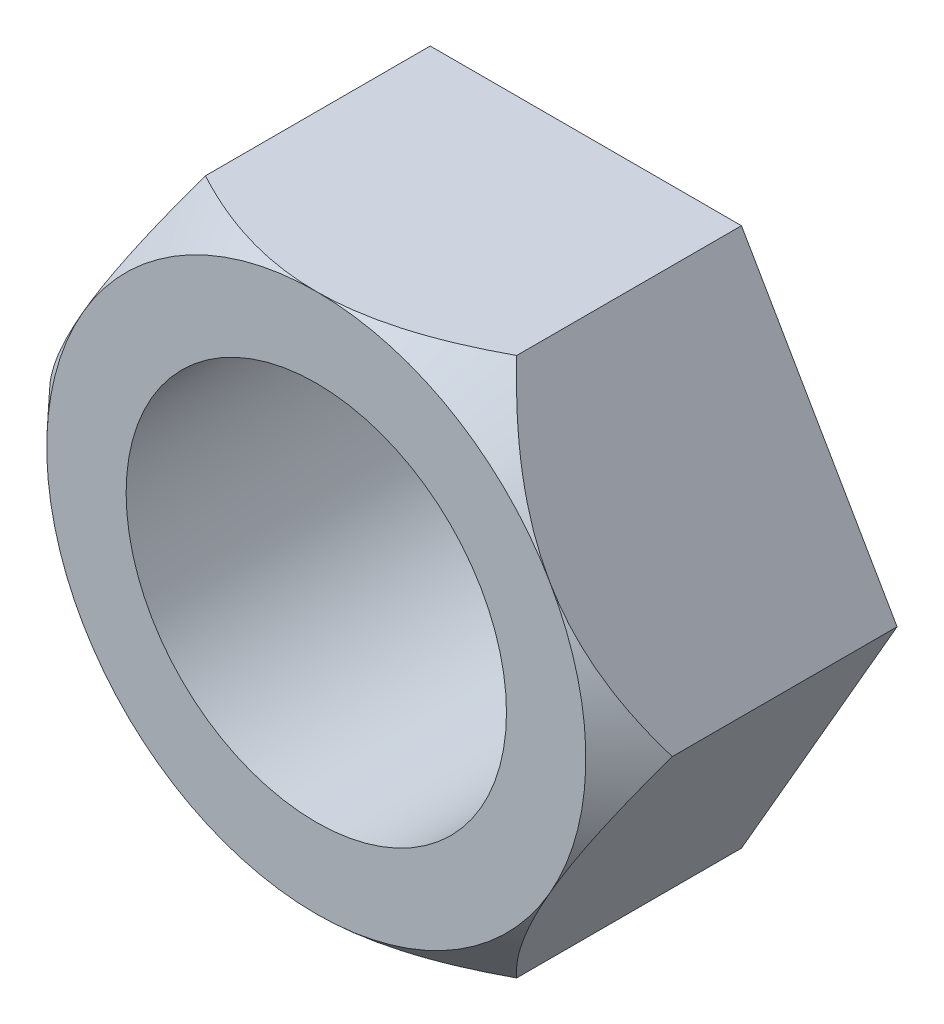
SolidWorks part; units mm, degrees
ref_plane "Alzado" through (0, 0, 0) normal (0, 0, 1) x (1, 0, 0)
ref_plane "Planta" through (0, 0, 0) normal (0, 1, 0) x (1, 0, 0)
ref_plane "Vista lateral" through (0, 0, 0) normal (1, 0, 0) x (0, 0, -1)
sketch "Croquis1" plane through (0, 0, 0) normal (0, 0, 1) x (1, 0, 0)
  line L1 (-10.3923, 0) -> (-5.1962, -9)
  line L2 (-5.1962, -9) -> (5.1962, -9)
  line L3 (5.1962, -9) -> (10.3923, 0)
  line L4 (10.3923, 0) -> (5.1962, 9)
  line L5 (5.1962, 9) -> (-5.1962, 9)
  line L6 (-5.1962, 9) -> (-10.3923, 0)
  circle A0 centre (0, 0) radius 9 construction
  circle A1 centre (0, 0) radius 6.35
  dimension "D2" = 12.7
  dimension "D1" = 18
extrude "Saliente-Extruir1" add sketch "Croquis1" along normal blind 9
sketch "Croquis2" plane through (0, 0, 9) normal (0, 0, 1) x (1, 0, 0)
  circle A0 centre (0, 0) radius 9
  circle A1 centre (-0.194, 0) radius 17.9502
extrude "Cortar-Extruir1" cut sketch "Croquis2" against normal blind 9 draft 43
